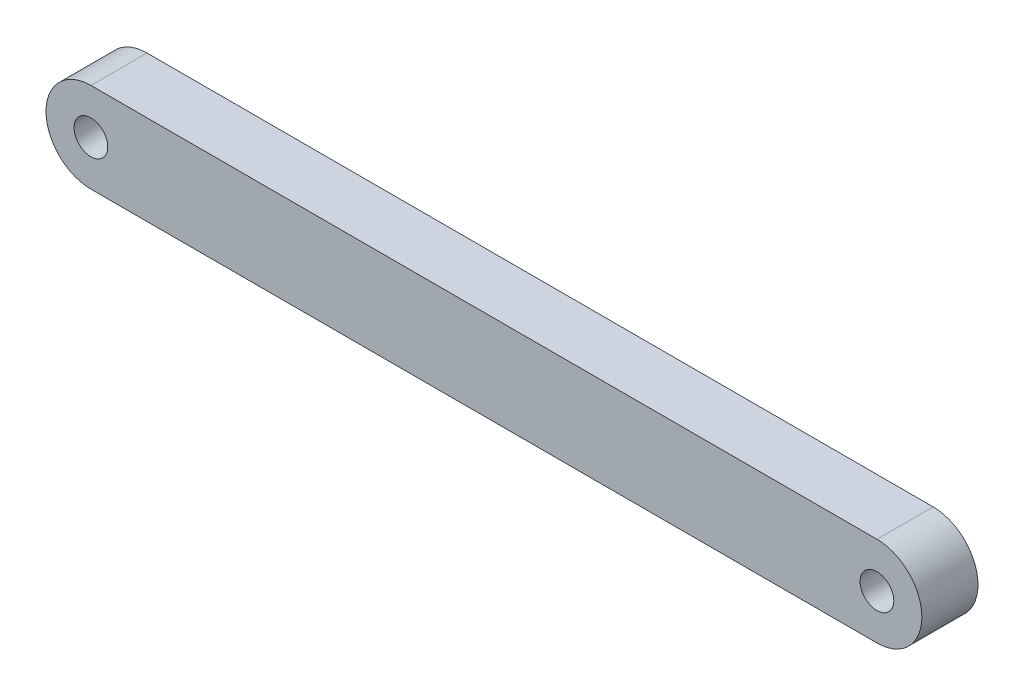
SolidWorks part; units mm, degrees
ref_plane "Front Plane" through (0, 0, 0) normal (0, 0, 1) x (1, 0, 0)
ref_plane "Top Plane" through (0, 0, 0) normal (0, 1, 0) x (1, 0, 0)
ref_plane "Right Plane" through (0, 0, 0) normal (1, 0, 0) x (0, 0, -1)
sketch "Sketch1" plane through (0, 0, 0) normal (0, 0, 1) x (1, 0, 0)
  line L0 (0, 0) -> (70, 0) construction
  line L1 (0, 4) -> (70, 4)
  line L2 (0, -4) -> (70, -4)
  arc A0 (0, 4) -> (0, -4) centre (0, 0) ccw
  arc A1 (70, -4) -> (70, 4) centre (70, 0) ccw
  circle A2 centre (0, 0) radius 1.5
  circle A3 centre (70, 0) radius 1.5
  point P3 (35, 0)
  dimension "D3" = 3
  dimension "3.15" = 3
  dimension "D1" = 70
  dimension "D2" = 8
extrude "Boss-Extrude1" add sketch "Sketch1" along normal blind 5
